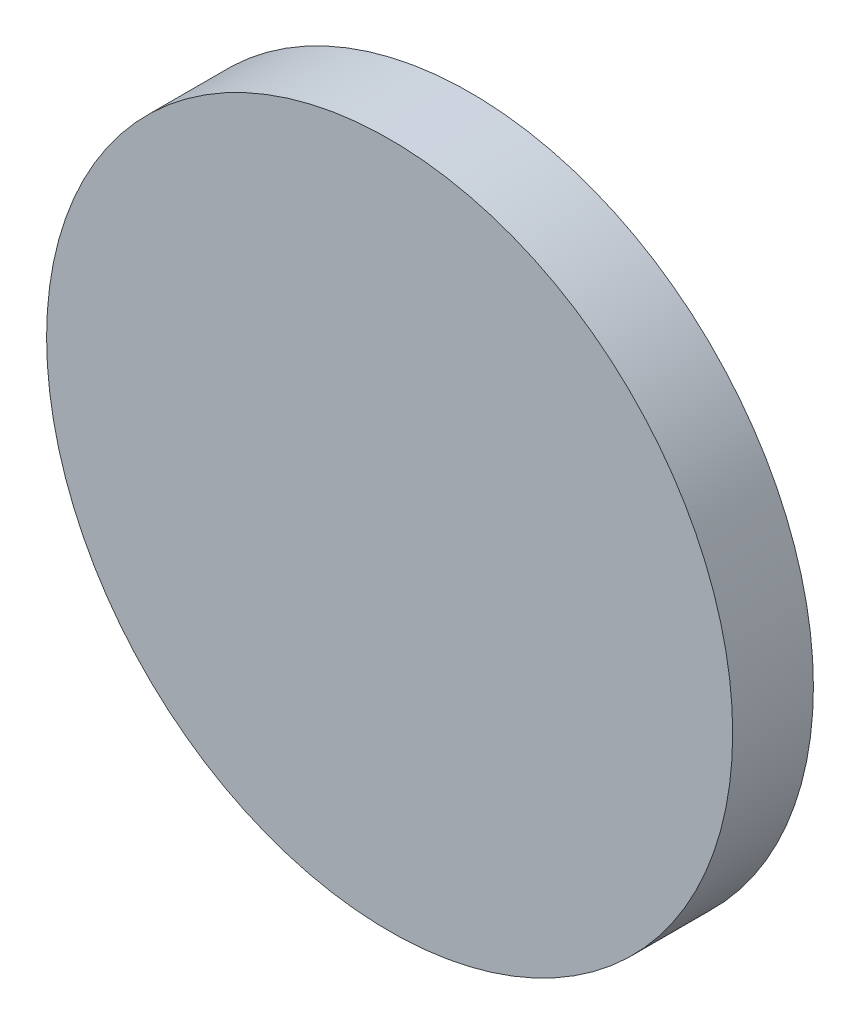
SolidWorks part; units mm, degrees
material "Glass"
ref_plane "Front Plane" through (0, 0, 0) normal (0, 0, 1) x (1, 0, 0)
ref_plane "Top Plane" through (0, 0, 0) normal (0, 1, 0) x (1, 0, 0)
ref_plane "Right Plane" through (0, 0, 0) normal (1, 0, 0) x (0, 0, -1)
sketch "Sketch1" plane through (0, 0, 0) normal (0, 0, 1) x (1, 0, 0)
  circle A0 centre (0, 0) radius 17
extrude "Boss-Extrude1" add sketch "Sketch1" along normal blind 4
